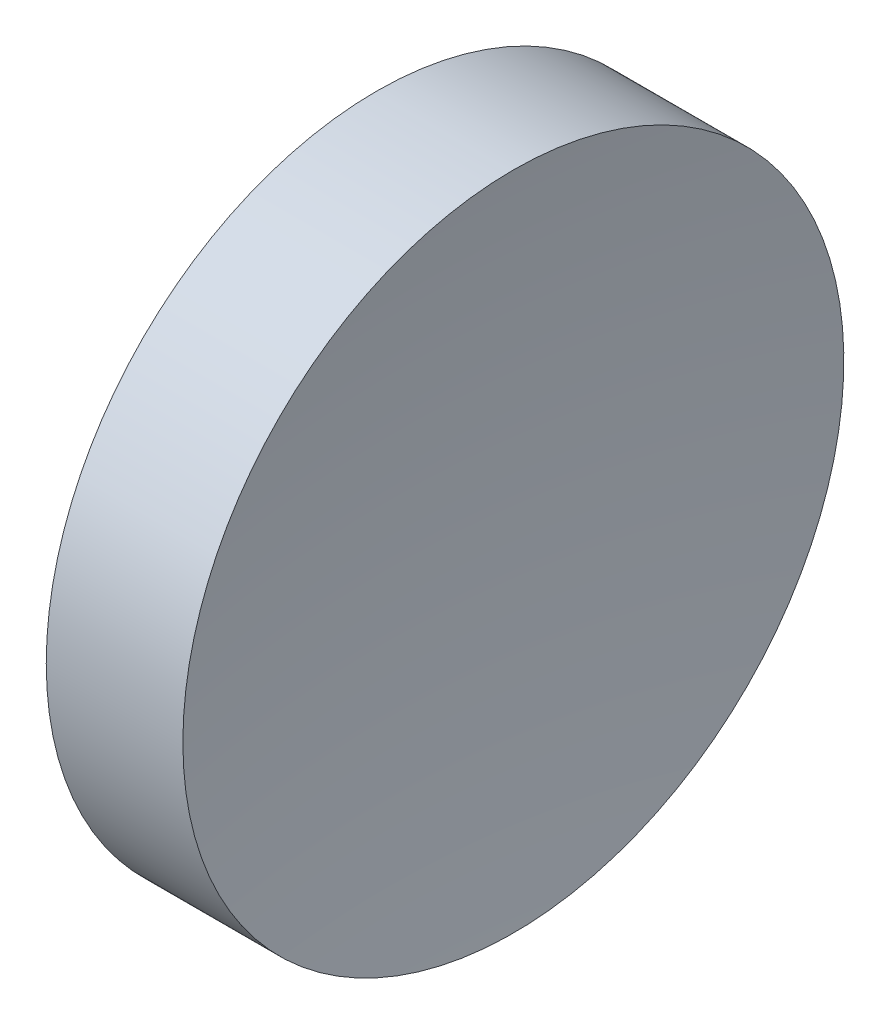
SolidWorks part; units mm, degrees
ref_plane "前视基准面" through (0, 0, 0) normal (0, 0, 1) x (1, 0, 0)
ref_plane "上视基准面" through (0, 0, 0) normal (0, 1, 0) x (1, 0, 0)
ref_plane "右视基准面" through (0, 0, 0) normal (1, 0, 0) x (0, 0, -1)
sketch "草图1" plane through (0, 0, 0) normal (0, 0, 1) x (1, 0, 0)
  line L0 (109.9369, 65.2226) -> (130.1809, 65.2226) construction
  line L1 (121.8527, 65.2226) -> (118.3527, 65.2226)
  line L3 (120.1027, 77.9226) -> (122.7277, 77.9226)
  line L4 (120.1027, 77.9226) -> (117.4777, 77.9226)
  arc A0 (118.3527, 65.2226) -> (117.4777, 77.9226) centre (25.7527, 65.2226) ccw
  arc A1 (122.7277, 77.9226) -> (121.8527, 65.2226) centre (214.4527, 65.2226) ccw
revolve "旋转1" add sketch "草图1" angle 360 about L0
